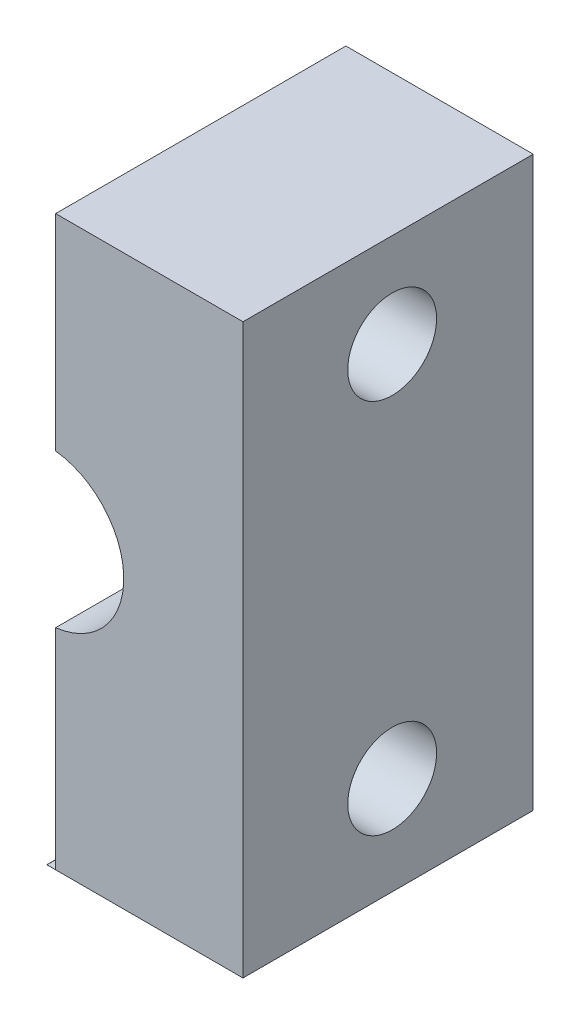
SolidWorks part; units mm, degrees
material "Pure Gold"
ref_plane "Front" through (0, 0, 0) normal (0, 0, 1) x (1, 0, 0)
ref_plane "Top" through (0, 0, 0) normal (0, 1, 0) x (1, 0, 0)
ref_plane "Right" through (0, 0, 0) normal (1, 0, 0) x (0, 0, -1)
sketch "Sketch4" plane through (0, 0, 0) normal (0, 0, 1) x (1, 0, 0)
  line L0 (0, -42.8625) -> (0, 41.275) construction
  line L1 (-49.15, -15.5) -> (-80.15, 15.5) construction
  line L2 (-80.15, -15.5) -> (-49.15, 15.5) construction
  line L3 (-39.925, 44.5615) -> (-39.925, -66.5635) construction
  line L4 (-71.275, 44.5615) -> (-71.275, -66.5635) construction
  line L8 (-62.05, 15.5) -> (-31.05, -15.5) construction
  line L9 (-31.05, 15.5) -> (-62.05, -15.5) construction
  line L11 (-31.05, 36.624) -> (-31.05, -53.8635) construction
  line L12 (43.75, 0) -> (-164.4633, 0) construction
  line L13 (-62.05, 36.624) -> (-62.05, -53.8635) construction
  line L14 (-49.15, 36.624) -> (-49.15, -53.8635) construction
  line L15 (-80.15, 36.624) -> (-80.15, -53.8635) construction
  line L16 (-113.2228, 15.5) -> (-0.2036, 15.5) construction
  line L17 (-113.2228, -15.5) -> (-0.2036, -15.5) construction
  line L18 (-25, -66.5635) -> (-25, 44.5615) construction
  line L19 (-68.1, -66.5635) -> (-68.1, 44.5615) construction
  line L20 (-43.1, 44.5615) -> (-43.1, -66.5635) construction
  line L21 (-86.2, -66.5635) -> (-86.2, 44.5615) construction
  line L22 (5.8397, -21.55) -> (-134.1626, -21.55) construction
  line L23 (5.8397, 21.55) -> (-134.1626, 21.55) construction
  line L24 (10.9249, -24.725) -> (-138.6228, -24.725) construction
  line L25 (10.9249, 24.725) -> (-138.6228, 24.725) construction
  line L26 (-89.375, 44.5615) -> (-89.375, -66.5635) construction
  line L27 (-21.825, 44.5615) -> (-21.825, -66.5635) construction
  circle A0 centre (0, 0) radius 12.7 construction
  circle A1 centre (0, 0) radius 15.875 construction
  circle A2 centre (0, 0) radius 9.46 construction
  circle A3 centre (-93.65, 0) radius 9.46 construction
  arc A4 (-93.65, 12.7) -> (-93.65, -12.7) centre (-93.65, 0) ccw construction
  circle A5 centre (27.27, 0) radius 9.46 construction
  circle A6 centre (27.27, 0) radius 12.7 construction
  circle A7 centre (-120.3675, 0) radius 9.46 construction
  circle A8 centre (-120.3675, 0) radius 12.7 construction
  point P3 (0, 0)
  point P6 (-49.15, -15.5)
  point P11 (-93.65, 0)
  point P12 (-49.15, 15.5)
  point P13 (-46.55, 0)
  point P14 (-80.15, 15.5)
  point P15 (-80.15, -15.5)
  point P61 (-64.65, 0)
  point P65 (27.27, 0)
  point P66 (-120.3675, 0)
  dimension "D20" = 3.175
  dimension "D18" = 29
  dimension "D26" = 73.82
  dimension "D27" = 64.65
  dimension "D2" = 31
  dimension "D3" = 25
  dimension "D4" = 31
  dimension "D5" = 21.825
  dimension "D6" = 15.5
  dimension "D7" = 15.5
  dimension "D8" = 6.05
  dimension "D9" = 6.05
  dimension "D10" = 6.05
  dimension "D11" = 6.05
  dimension "D12" = 6.05
  dimension "D13" = 6.05
  dimension "D14" = 3.175
  dimension "D15" = 3.175
  dimension "D16" = 3.175
  dimension "D17" = 3.175
  dimension "D19" = 3.175
  dimension "D21" = 3.175
  dimension "D22" = 46.55
  dimension "D23" = 47.1
  dimension "D24" = 58.32
  dimension "D25" = 147.6375
sketch "Sketch5" plane through (0, 0, 0) normal (0, 0, 1) x (1, 0, 0)
  line L0 (-46.55, 1.6) -> (-46.55, -2.6) construction
  line L4 (-46.55, -2.6) -> (-46.55, -9.6636)
  line L5 (-46.55, 9.525) -> (-39.925, 9.525)
  line L7 (-39.925, 44.5615) -> (-39.925, -66.5635) construction
  line L8 (-39.925, -9.6636) -> (-39.925, 9.525)
  line L9 (-46.55, -9.6636) -> (-39.925, -9.6636)
  line L13 (-46.55, 9.525) -> (-46.55, 2.6)
  circle A0 centre (-46.55, 0) radius 2.6 construction
  arc A1 (-46.55, 2.6) -> (-46.55, -2.6) centre (-46.55, 0) cw
extrude "Extrude1" add sketch "Sketch5" along normal blind 9.8
sketch "Sketch7" plane through (-39.925, 0, 0) normal (1, 0, 0) x (0, 0, -1)
  circle A0 centre (-4.7625, 6.35) radius 1.5
  circle A1 centre (-4.7625, -6.35) radius 1.5
extrude "Extrude3" cut sketch "Sketch7" against normal up to surface (6.625 mm away) up to face at (-46.55, 6.0625, 4.9)
sketch "Sketch9" plane through (0, 0, 9.8) normal (0, 0, 1) x (1, 0, 0)
  line L0 (-46.55, 9.525) -> (-46.55, -9.6636)
  line L1 (-46.25, 9.525) -> (-46.25, -9.6636)
  line L2 (-39.925, 9.525) -> (-46.55, 9.525) construction
  line L3 (-46.55, -9.6636) -> (-39.925, -9.6636) construction
  line L4 (-46.55, 9.525) -> (-46.25, 9.525)
  line L5 (-46.55, -9.6636) -> (-46.5392, -9.658)
  line L6 (-46.5392, -9.658) -> (-46.25, -9.6636)
  dimension "D1" = 0.3
extrude "Extrude4" cut sketch "Sketch9" against normal through all
